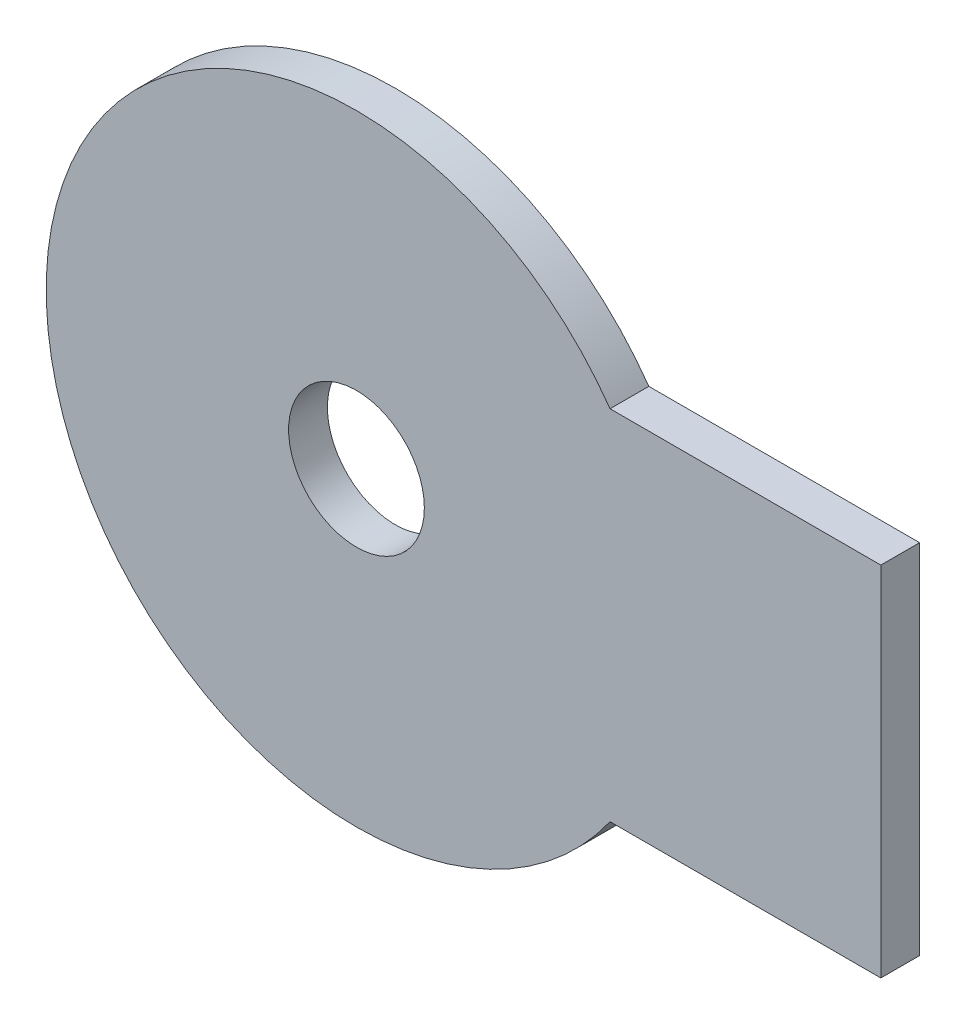
SolidWorks part; units mm, degrees
material "6061-T6 (SS)"
ref_plane "Front Plane" through (0, 0, 0) normal (0, 0, 1) x (1, 0, 0)
ref_plane "Top Plane" through (0, 0, 0) normal (0, 1, 0) x (1, 0, 0)
ref_plane "Right Plane" through (0, 0, 0) normal (1, 0, 0) x (0, 0, -1)
sketch "Sketch1" plane through (0, 0, 0) normal (0, 0, 1) x (1, 0, 0)
  line L0 (0, 0) -> (127.3638, 0) construction
  line L2 (171.6936, 58.5483) -> (83.034, 58.5483)
  line L3 (171.6936, 58.5483) -> (171.6936, -58.5483)
  line L4 (171.6936, -58.5483) -> (83.034, -58.5483)
  line L5 (83.034, 58.5483) -> (83.034, -58.5483)
  line L6 (171.6936, 58.5483) -> (83.034, -58.5483) construction
  line L7 (171.6936, -58.5483) -> (83.034, 58.5483) construction
  circle A0 centre (0, 0) radius 101.6
  circle A1 centre (0, 0) radius 22.225
  dimension "D1" = 203.2
  dimension "D2" = 44.45
extrude "Boss-Extrude1" add sketch "Sketch1" along normal blind 12.7 contours L5 A0 | L5 A0 | A0 L4 L3 L2
